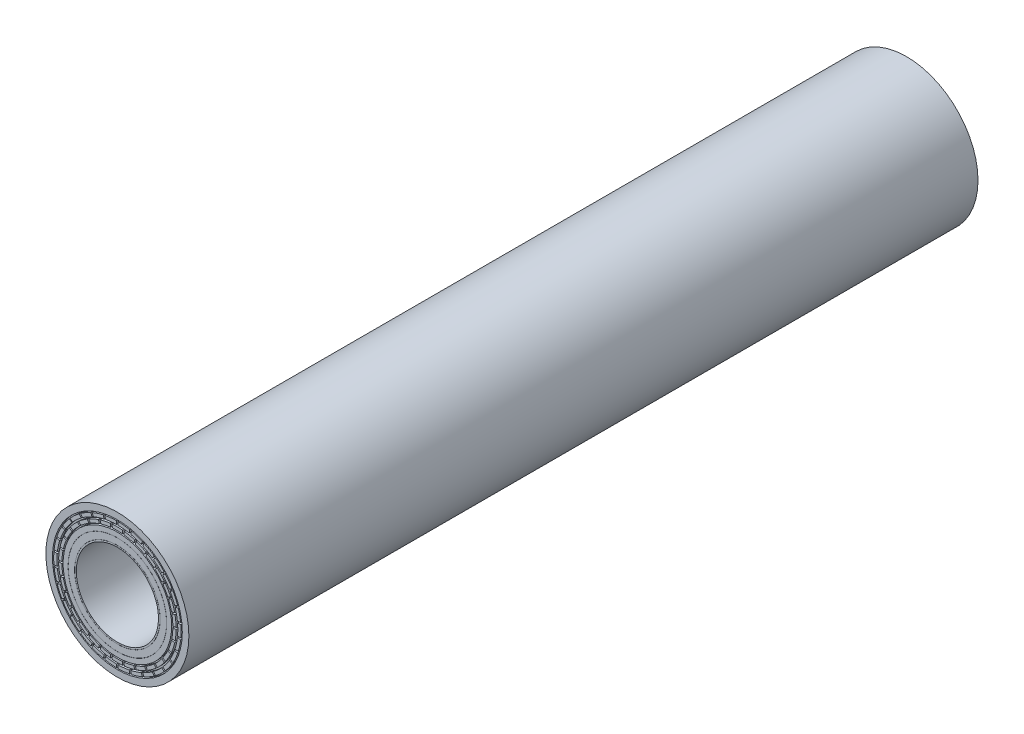
SolidWorks part; units mm, degrees
ref_plane "Front Plane" through (0, 0, 0) normal (0, 0, 1) x (1, 0, 0)
ref_plane "Top Plane" through (0, 0, 0) normal (0, 1, 0) x (1, 0, 0)
ref_plane "Right Plane" through (0, 0, 0) normal (1, 0, 0) x (0, 0, -1)
sketch "Sketch1" plane through (0, 0, 0) normal (0, 0, 1) x (1, 0, 0)
  circle A1 centre (0, 87) radius 87
  dimension "D1" = 87
  dimension "D2" = 0
  dimension "D3" = 174
extrude "Boss-Extrude1" add sketch "Sketch1" against normal blind 960
sketch "Sketch2" plane through (0, 0, 0) normal (0, 0, 1) x (1, 0, 0)
  circle A0 centre (0, 87) radius 52
  dimension "D1" = 104
extrude "Cut-Extrude1" cut sketch "Sketch2" against normal through all
sketch "Sketch3" plane through (0, 0, 0) normal (0, 0, 1) x (1, 0, 0)
  circle A0 centre (0, 87) radius 77.5
  circle A2 centre (0, 87) radius 87 construction
  circle A3 centre (0, 87) radius 60
  circle A4 centre (0, 87) radius 66
  circle A5 centre (0, 87) radius 67.5
  circle A6 centre (0, 87) radius 71.5
  circle A7 centre (0, 87) radius 73.5
  circle A8 centre (0, 87) radius 79
  dimension "D1" = 0
  dimension "D2" = 155
  dimension "D3" = 120
  dimension "D4" = 132
  dimension "D5" = 135
  dimension "D6" = 143
  dimension "D7" = 147
  dimension "D8" = 158
extrude "Cut-Extrude2" cut sketch "Sketch3" against normal blind 3 contours A8 A0 | A7 A6 | A5 A4
sketch "Sketch4" plane through (0, 0, 0) normal (0, 0, 1) x (1, 0, 0)
  circle A0 centre (0, 87) radius 60
  dimension "D1" = 120
split line "Split Line1"
ref_plane "Plane1" through (0, 0, -480) normal (0, 0, 1) x (1, 0, 0)
mirror "Mirror2" about plane through (0, 0, -480) normal (0, 0, 1) of "Cut-Extrude2"
sketch "Sketch5" plane through (0, 0, -960) normal (0, 0, -1) x (-1, 0, 0)
  circle A0 centre (0, 87) radius 60
  dimension "D1" = 120
split line "Split Line2"
sketch "Sketch7" plane through (0, 0, 0) normal (0, 0, 1) x (1, 0, 0)
  line L0 (0, 9) -> (0, 14.5)
  line L1 (-17.1953, 10.9124) -> (-16.0517, 16.2922)
  line L2 (-15.239, 10.4966) -> (-14.0954, 15.8764)
  line L3 (-16.2171, 10.7045) -> (-15.0736, 16.0843)
  line L4 (-16.0517, 16.2922) -> (-14.0954, 15.8764)
  line L5 (-17.1953, 10.9124) -> (-15.239, 10.4966)
  line L6 (-32.639, 16.1502) -> (-30.402, 21.1747)
  line L7 (-30.8119, 15.3367) -> (-28.5749, 20.3612)
  line L8 (-31.7255, 15.7435) -> (-29.4884, 20.768)
  line L9 (-30.402, 21.1747) -> (-28.5749, 20.3612)
  line L10 (-32.639, 16.1502) -> (-30.8119, 15.3367)
  line L11 (-46.6563, 24.4845) -> (-43.4234, 28.9341)
  line L12 (-45.0382, 23.3089) -> (-41.8054, 27.7585)
  line L13 (-45.8472, 23.8967) -> (-42.6144, 28.3463)
  line L14 (-43.4234, 28.9341) -> (-41.8054, 27.7585)
  line L15 (-46.6563, 24.4845) -> (-45.0382, 23.3089)
  line L16 (-58.6344, 35.551) -> (-54.5471, 39.2312)
  line L17 (-57.2962, 34.0647) -> (-53.2089, 37.7449)
  line L18 (-57.9653, 34.8078) -> (-53.878, 38.488)
  line L19 (-54.5471, 39.2312) -> (-53.2089, 37.7449)
  line L20 (-58.6344, 35.551) -> (-57.2962, 34.0647)
  line L21 (-68.05, 48.866) -> (-63.2868, 51.616)
  line L22 (-67.05, 47.134) -> (-62.2868, 49.884)
  line L23 (-67.55, 48) -> (-62.7868, 50.75)
  line L24 (-63.2868, 51.616) -> (-62.2868, 49.884)
  line L25 (-68.05, 48.866) -> (-67.05, 47.134)
  line L26 (-74.4914, 63.8477) -> (-69.2606, 65.5473)
  line L27 (-73.8734, 61.9456) -> (-68.6426, 63.6452)
  line L28 (-74.1824, 62.8967) -> (-68.9516, 64.5963)
  line L29 (-69.2606, 65.5473) -> (-68.6426, 63.6452)
  line L31 (-74.4914, 63.8477) -> (-73.8734, 61.9456)
  line L32 (-77.6772, 79.8413) -> (-72.2074, 80.4162)
  line L33 (-77.4682, 77.8523) -> (-71.9983, 78.4272)
  line L34 (-77.5727, 78.8468) -> (-72.1028, 79.4217)
  line L35 (-72.2074, 80.4162) -> (-71.9983, 78.4272)
  line L36 (-77.6772, 79.8413) -> (-77.4682, 77.8523)
  line L37 (-77.4682, 96.1477) -> (-71.9983, 95.5728)
  line L38 (-77.6772, 94.1587) -> (-72.2074, 93.5838)
  line L39 (-77.5727, 95.1532) -> (-72.1028, 94.5783)
  line L40 (-71.9983, 95.5728) -> (-72.2074, 93.5838)
  line L41 (-77.4682, 96.1477) -> (-77.6772, 94.1587)
  line L42 (-73.8734, 112.0544) -> (-68.6426, 110.3548)
  line L43 (-74.4914, 110.1523) -> (-69.2606, 108.4527)
  line L44 (-74.1824, 111.1033) -> (-68.9516, 109.4037)
  line L45 (-68.6426, 110.3548) -> (-69.2606, 108.4527)
  line L46 (-73.8734, 112.0544) -> (-74.4914, 110.1523)
  line L47 (-67.05, 126.866) -> (-62.2868, 124.116)
  line L48 (-68.05, 125.134) -> (-63.2868, 122.384)
  line L49 (-67.55, 126) -> (-62.7868, 123.25)
  line L50 (-62.2868, 124.116) -> (-63.2868, 122.384)
  line L51 (-67.05, 126.866) -> (-68.05, 125.134)
  line L52 (-57.2962, 139.9353) -> (-53.2089, 136.2551)
  line L53 (-58.6344, 138.449) -> (-54.5471, 134.7688)
  line L54 (-57.9653, 139.1922) -> (-53.878, 135.512)
  line L55 (-53.2089, 136.2551) -> (-54.5471, 134.7688)
  line L56 (-57.2962, 139.9353) -> (-58.6344, 138.449)
  line L57 (-45.0382, 150.6911) -> (-41.8054, 146.2415)
  line L58 (-46.6563, 149.5155) -> (-43.4234, 145.0659)
  line L59 (-45.8472, 150.1033) -> (-42.6144, 145.6537)
  line L61 (-41.8054, 146.2415) -> (-43.4234, 145.0659)
  line L62 (-45.0382, 150.6911) -> (-46.6563, 149.5155)
  line L63 (-30.8119, 158.6633) -> (-28.5749, 153.6388)
  line L64 (-32.639, 157.8498) -> (-30.402, 152.8253)
  line L65 (-31.7255, 158.2565) -> (-29.4884, 153.232)
  line L66 (-28.5749, 153.6388) -> (-30.402, 152.8253)
  line L67 (-30.8119, 158.6633) -> (-32.639, 157.8498)
  line L68 (-15.239, 163.5034) -> (-14.0954, 158.1236)
  line L69 (-17.1953, 163.0876) -> (-16.0517, 157.7078)
  line L70 (-16.2171, 163.2955) -> (-15.0736, 157.9157)
  line L71 (-14.0954, 158.1236) -> (-16.0517, 157.7078)
  line L72 (-15.239, 163.5034) -> (-17.1953, 163.0876)
  line L73 (1, 165) -> (1, 159.5)
  line L74 (-1, 165) -> (-1, 159.5)
  line L75 (0, 165) -> (0, 159.5)
  line L76 (1, 159.5) -> (-1, 159.5)
  line L77 (1, 165) -> (-1, 165)
  line L78 (17.1953, 163.0876) -> (16.0517, 157.7078)
  line L79 (15.239, 163.5034) -> (14.0954, 158.1236)
  line L80 (16.2171, 163.2955) -> (15.0736, 157.9157)
  line L81 (16.0517, 157.7078) -> (14.0954, 158.1236)
  line L82 (17.1953, 163.0876) -> (15.239, 163.5034)
  line L83 (32.639, 157.8498) -> (30.402, 152.8253)
  line L84 (30.8119, 158.6633) -> (28.5749, 153.6388)
  line L85 (31.7255, 158.2565) -> (29.4884, 153.232)
  line L86 (30.402, 152.8253) -> (28.5749, 153.6388)
  line L87 (32.639, 157.8498) -> (30.8119, 158.6633)
  line L88 (46.6563, 149.5155) -> (43.4234, 145.0659)
  line L89 (45.0382, 150.6911) -> (41.8054, 146.2415)
  line L90 (45.8472, 150.1033) -> (42.6144, 145.6537)
  line L91 (1, 9) -> (1, 14.5)
  line L92 (-1, 9) -> (-1, 14.5)
  line L93 (-1, 14.5) -> (1, 14.5)
  line L94 (-1, 9) -> (1, 9)
  line L95 (43.4234, 145.0659) -> (41.8054, 146.2415)
  line L96 (46.6563, 149.5155) -> (45.0382, 150.6911)
  line L97 (58.6344, 138.449) -> (54.5471, 134.7688)
  line L98 (57.2962, 139.9353) -> (53.2089, 136.2551)
  line L99 (57.9653, 139.1922) -> (53.878, 135.512)
  line L100 (54.5471, 134.7688) -> (53.2089, 136.2551)
  line L101 (58.6344, 138.449) -> (57.2962, 139.9353)
  line L102 (68.05, 125.134) -> (63.2868, 122.384)
  line L103 (67.05, 126.866) -> (62.2868, 124.116)
  line L104 (67.55, 126) -> (62.7868, 123.25)
  line L105 (63.2868, 122.384) -> (62.2868, 124.116)
  line L106 (68.05, 125.134) -> (67.05, 126.866)
  line L107 (74.4914, 110.1523) -> (69.2606, 108.4527)
  line L108 (73.8734, 112.0544) -> (68.6426, 110.3548)
  line L109 (74.1824, 111.1033) -> (68.9516, 109.4037)
  line L110 (69.2606, 108.4527) -> (68.6426, 110.3548)
  line L111 (74.4914, 110.1523) -> (73.8734, 112.0544)
  line L112 (77.6772, 94.1587) -> (72.2074, 93.5838)
  line L113 (77.4682, 96.1477) -> (71.9983, 95.5728)
  line L114 (77.5727, 95.1532) -> (72.1028, 94.5783)
  line L115 (72.2074, 93.5838) -> (71.9983, 95.5728)
  line L116 (77.6772, 94.1587) -> (77.4682, 96.1477)
  line L117 (77.4682, 77.8523) -> (71.9983, 78.4272)
  line L118 (77.6772, 79.8413) -> (72.2074, 80.4162)
  line L119 (77.5727, 78.8468) -> (72.1028, 79.4217)
  line L120 (71.9983, 78.4272) -> (72.2074, 80.4162)
  line L121 (77.4682, 77.8523) -> (77.6772, 79.8413)
  line L122 (73.8734, 61.9456) -> (68.6426, 63.6452)
  line L123 (74.4914, 63.8477) -> (69.2606, 65.5473)
  line L124 (74.1824, 62.8967) -> (68.9516, 64.5963)
  line L125 (68.6426, 63.6452) -> (69.2606, 65.5473)
  line L126 (73.8734, 61.9456) -> (74.4914, 63.8477)
  line L127 (67.05, 47.134) -> (62.2868, 49.884)
  line L128 (68.05, 48.866) -> (63.2868, 51.616)
  line L129 (67.55, 48) -> (62.7868, 50.75)
  line L130 (62.2868, 49.884) -> (63.2868, 51.616)
  line L131 (67.05, 47.134) -> (68.05, 48.866)
  line L132 (57.2962, 34.0647) -> (53.2089, 37.7449)
  line L133 (58.6344, 35.551) -> (54.5471, 39.2312)
  line L134 (57.9653, 34.8078) -> (53.878, 38.488)
  line L135 (53.2089, 37.7449) -> (54.5471, 39.2312)
  line L136 (57.2962, 34.0647) -> (58.6344, 35.551)
  line L137 (45.0382, 23.3089) -> (41.8054, 27.7585)
  line L138 (46.6563, 24.4845) -> (43.4234, 28.9341)
  line L139 (45.8472, 23.8967) -> (42.6144, 28.3463)
  line L140 (41.8054, 27.7585) -> (43.4234, 28.9341)
  line L141 (45.0382, 23.3089) -> (46.6563, 24.4845)
  line L142 (30.8119, 15.3367) -> (28.5749, 20.3612)
  line L143 (32.639, 16.1502) -> (30.402, 21.1747)
  line L144 (31.7255, 15.7435) -> (29.4884, 20.768)
  line L145 (28.5749, 20.3612) -> (30.402, 21.1747)
  line L146 (30.8119, 15.3367) -> (32.639, 16.1502)
  line L147 (15.239, 10.4966) -> (14.0954, 15.8764)
  line L148 (17.1953, 10.9124) -> (16.0517, 16.2922)
  line L149 (16.2171, 10.7045) -> (15.0736, 16.0843)
  line L150 (14.0954, 15.8764) -> (16.0517, 16.2922)
  line L151 (15.239, 10.4966) -> (17.1953, 10.9124)
  circle A5 centre (0, 87) radius 71.5 construction
  point P72 (0, 87)
  point P186 (0, 87)
  dimension "D1" = 1
  dimension "D2" = 1
  dimension "D3" = 72.5
  dimension "D4" = 30
extrude "Cut-Extrude5" cut sketch "Sketch7" against normal blind 3 contours L1 L5 L3 L4 | L3 L5 L2 L4 | L147 L151 L149 L150 | L149 L151 L148 L150 | L142 L146 L144 L145 | L144 L146 L143 L145 | L6 L10 L8 L9 | L8 L10 L7 L9 | L11 L15 L13 L14 | L13 L15 L12 L14 | L16 L20 L18 L19 | L21 L25 L23 L24 | L23 L25 L22 L24 | L26 L31 L28 L29 | L28 L31 L27 L29 | L32 L36 L34 L35 | L34 L36 L33 L35 | L37 L41 L39 L40 | L39 L41 L38 L40 | L42 L46 L44 L45 | L44 L46 L43 L45 | L49 L51 L48 L50 | L47 L51 L49 L50 | L54 L56 L53 L55 | L59 L62 L58 L61 | L57 L62 L59 L61 | L65 L67 L64 L66 | L63 L67 L65 L66 | L70 L72 L69 L71 | L68 L72 L70 L71 | L75 L77 L74 L76 | L73 L77 L75 L76 | L80 L82 L79 L81 | L78 L82 L80 L81 | L85 L87 L84 L86 | L83 L87 L85 L86 | L90 L96 L89 L95 | L88 L96 L90 L95 | L99 L101 L98 L100 | L97 L101 L99 L100 | L104 L106 L103 L105 | L102 L106 L104 L105 | L109 L111 L108 L110 | L107 L111 L109 L110 | L114 L116 L113 L115 | L112 L116 L114 L115 | L124 L126 L123 L125 | L122 L126 L124 L125 | L119 L121 L118 L120 | L117 L121 L119 L120 | L129 L131 L128 L130 | L127 L131 L129 L130 | L134 L136 L133 L135 | L132 L136 L134 L135 | L137 L141 L139 L140 | L139 L141 L138 L140 | L92 L94 L0 L93 | L0 L94 L91 L93
mirror "Mirror3" about plane through (0, 0, -480) normal (0, 0, 1) of "Cut-Extrude5"
sketch "Sketch8" plane through (0, 0, 0) normal (0, 0, 1) x (1, 0, 0)
  line L0 (-66.5, 88) -> (-72, 88)
  line L1 (-72, 88) -> (-72, 86)
  line L2 (-66.5, 86) -> (-72, 86)
  line L3 (-66.5, 88) -> (-66.5, 86)
  line L4 (-64.8389, 101.8043) -> (-70.2187, 102.9478)
  line L5 (-72, 87) -> (-66.5, 87) construction
  line L6 (-65.2547, 99.848) -> (-70.6345, 100.9915)
  line L7 (-64.8389, 101.8043) -> (-65.2547, 99.848)
  line L8 (-70.2187, 102.9478) -> (-70.6345, 100.9915)
  line L9 (-60.344, 114.9615) -> (-65.3685, 117.1986)
  line L10 (-61.1575, 113.1344) -> (-66.182, 115.3715)
  line L11 (-60.344, 114.9615) -> (-61.1575, 113.1344)
  line L12 (-65.3685, 117.1986) -> (-66.182, 115.3715)
  line L13 (-53.2118, 126.8967) -> (-57.6614, 130.1296)
  line L14 (-54.3874, 125.2787) -> (-58.837, 128.5115)
  line L15 (-53.2118, 126.8967) -> (-54.3874, 125.2787)
  line L16 (-57.6614, 130.1296) -> (-58.837, 128.5115)
  line L17 (-43.754, 137.0883) -> (-47.4343, 141.1756)
  line L18 (-45.2403, 135.75) -> (-48.9205, 139.8373)
  line L19 (-43.754, 137.0883) -> (-45.2403, 135.75)
  line L20 (-47.4343, 141.1756) -> (-48.9205, 139.8373)
  line L21 (-32.384, 145.0907) -> (-35.134, 149.8538)
  line L22 (-34.116, 144.0907) -> (-36.866, 148.8538)
  line L23 (-32.384, 145.0907) -> (-34.116, 144.0907)
  line L24 (-35.134, 149.8538) -> (-36.866, 148.8538)
  line L25 (-19.5986, 150.5543) -> (-21.2982, 155.7851)
  line L26 (-21.5007, 149.9362) -> (-23.2003, 155.1671)
  line L27 (-19.5986, 150.5543) -> (-21.5007, 149.9362)
  line L28 (-21.2982, 155.7851) -> (-23.2003, 155.1671)
  line L29 (-5.9566, 153.2402) -> (-6.5315, 158.7101)
  line L30 (-7.9457, 153.0312) -> (-8.5206, 158.501)
  line L31 (-5.9566, 153.2402) -> (-7.9457, 153.0312)
  line L32 (-6.5315, 158.7101) -> (-8.5206, 158.501)
  line L33 (7.9457, 153.0312) -> (8.5206, 158.501)
  line L34 (5.9566, 153.2402) -> (6.5315, 158.7101)
  line L35 (7.9457, 153.0312) -> (5.9566, 153.2402)
  line L36 (8.5206, 158.501) -> (6.5315, 158.7101)
  line L37 (21.5007, 149.9362) -> (23.2003, 155.1671)
  line L38 (19.5986, 150.5543) -> (21.2982, 155.7851)
  line L39 (21.5007, 149.9362) -> (19.5986, 150.5543)
  line L40 (23.2003, 155.1671) -> (21.2982, 155.7851)
  line L41 (34.116, 144.0907) -> (36.866, 148.8538)
  line L42 (32.384, 145.0907) -> (35.134, 149.8538)
  line L43 (34.116, 144.0907) -> (32.384, 145.0907)
  line L44 (36.866, 148.8538) -> (35.134, 149.8538)
  line L45 (45.2403, 135.75) -> (48.9205, 139.8373)
  line L46 (43.754, 137.0883) -> (47.4343, 141.1756)
  line L47 (45.2403, 135.75) -> (43.754, 137.0883)
  line L48 (48.9205, 139.8373) -> (47.4343, 141.1756)
  line L49 (54.3874, 125.2787) -> (58.837, 128.5115)
  line L50 (53.2118, 126.8967) -> (57.6614, 130.1296)
  line L51 (54.3874, 125.2787) -> (53.2118, 126.8967)
  line L52 (58.837, 128.5115) -> (57.6614, 130.1296)
  line L53 (61.1575, 113.1344) -> (66.182, 115.3715)
  line L54 (60.344, 114.9615) -> (65.3685, 117.1986)
  line L55 (61.1575, 113.1344) -> (60.344, 114.9615)
  line L56 (66.182, 115.3715) -> (65.3685, 117.1986)
  line L57 (65.2547, 99.848) -> (70.6345, 100.9915)
  line L58 (64.8389, 101.8043) -> (70.2187, 102.9478)
  line L59 (65.2547, 99.848) -> (64.8389, 101.8043)
  line L60 (70.6345, 100.9915) -> (70.2187, 102.9478)
  line L61 (66.5, 86) -> (72, 86)
  line L62 (66.5, 88) -> (72, 88)
  line L63 (66.5, 86) -> (66.5, 88)
  line L64 (72, 86) -> (72, 88)
  line L65 (64.8389, 72.1957) -> (70.2187, 71.0522)
  line L66 (65.2547, 74.152) -> (70.6345, 73.0085)
  line L67 (64.8389, 72.1957) -> (65.2547, 74.152)
  line L68 (70.2187, 71.0522) -> (70.6345, 73.0085)
  line L69 (60.344, 59.0385) -> (65.3685, 56.8014)
  line L70 (61.1575, 60.8656) -> (66.182, 58.6285)
  line L71 (60.344, 59.0385) -> (61.1575, 60.8656)
  line L72 (65.3685, 56.8014) -> (66.182, 58.6285)
  line L73 (53.2118, 47.1033) -> (57.6614, 43.8704)
  line L74 (54.3874, 48.7213) -> (58.837, 45.4885)
  line L75 (53.2118, 47.1033) -> (54.3874, 48.7213)
  line L76 (57.6614, 43.8704) -> (58.837, 45.4885)
  line L77 (43.754, 36.9117) -> (47.4343, 32.8244)
  line L78 (45.2403, 38.25) -> (48.9205, 34.1627)
  line L79 (43.754, 36.9117) -> (45.2403, 38.25)
  line L80 (47.4343, 32.8244) -> (48.9205, 34.1627)
  line L81 (32.384, 28.9093) -> (35.134, 24.1462)
  line L82 (34.116, 29.9093) -> (36.866, 25.1462)
  line L83 (32.384, 28.9093) -> (34.116, 29.9093)
  line L84 (35.134, 24.1462) -> (36.866, 25.1462)
  line L85 (19.5986, 23.4457) -> (21.2982, 18.2149)
  line L86 (21.5007, 24.0638) -> (23.2003, 18.8329)
  line L87 (19.5986, 23.4457) -> (21.5007, 24.0638)
  line L88 (21.2982, 18.2149) -> (23.2003, 18.8329)
  line L89 (5.9566, 20.7598) -> (6.5315, 15.2899)
  line L90 (7.9457, 20.9688) -> (8.5206, 15.499)
  line L91 (5.9566, 20.7598) -> (7.9457, 20.9688)
  line L92 (6.5315, 15.2899) -> (8.5206, 15.499)
  line L93 (-7.9457, 20.9688) -> (-8.5206, 15.499)
  line L94 (-5.9566, 20.7598) -> (-6.5315, 15.2899)
  line L95 (-7.9457, 20.9688) -> (-5.9566, 20.7598)
  line L96 (-8.5206, 15.499) -> (-6.5315, 15.2899)
  line L97 (-21.5007, 24.0638) -> (-23.2003, 18.8329)
  line L98 (-19.5986, 23.4457) -> (-21.2982, 18.2149)
  line L99 (-21.5007, 24.0638) -> (-19.5986, 23.4457)
  line L100 (-23.2003, 18.8329) -> (-21.2982, 18.2149)
  line L101 (-34.116, 29.9093) -> (-36.866, 25.1462)
  line L102 (-32.384, 28.9093) -> (-35.134, 24.1462)
  line L103 (-34.116, 29.9093) -> (-32.384, 28.9093)
  line L104 (-36.866, 25.1462) -> (-35.134, 24.1462)
  line L105 (-45.2403, 38.25) -> (-48.9205, 34.1627)
  line L106 (-43.754, 36.9117) -> (-47.4343, 32.8244)
  line L107 (-45.2403, 38.25) -> (-43.754, 36.9117)
  line L108 (-48.9205, 34.1627) -> (-47.4343, 32.8244)
  line L109 (-54.3874, 48.7213) -> (-58.837, 45.4885)
  line L110 (-53.2118, 47.1033) -> (-57.6614, 43.8704)
  line L111 (-54.3874, 48.7213) -> (-53.2118, 47.1033)
  line L112 (-58.837, 45.4885) -> (-57.6614, 43.8704)
  line L113 (-61.1575, 60.8656) -> (-66.182, 58.6285)
  line L114 (-60.344, 59.0385) -> (-65.3685, 56.8014)
  line L115 (-61.1575, 60.8656) -> (-60.344, 59.0385)
  line L116 (-66.182, 58.6285) -> (-65.3685, 56.8014)
  line L117 (-65.2547, 74.152) -> (-70.6345, 73.0085)
  line L118 (-64.8389, 72.1957) -> (-70.2187, 71.0522)
  line L119 (-65.2547, 74.152) -> (-64.8389, 72.1957)
  line L120 (-70.6345, 73.0085) -> (-70.2187, 71.0522)
  point P127 (0, 87)
  dimension "D1" = 30
extrude "Cut-Extrude6" cut sketch "Sketch8" against normal blind 3
mirror "Mirror4" about plane through (0, 0, -480) normal (0, 0, 1) of "Cut-Extrude6"
sketch "Sketch9" plane through (0, 0, 0) normal (0, 0, 1) x (1, 0, 0)
  circle A1 centre (0, 87) radius 50
  circle A2 centre (0, 87) radius 52 construction
  circle A3 centre (0, 87) radius 52
  dimension "D1" = 100
extrude "Boss-Extrude2" add sketch "Sketch9" against normal blind 960
sketch "Sketch10" plane through (0, 0, 0) normal (0, 0, 1) x (1, 0, 0)
  circle A0 centre (0, 87) radius 52
  circle A1 centre (0, 87) radius 51.9
  dimension "D1" = 104
  dimension "D2" = 0.1
sketch "Sketch11" plane through (0, 0, -960) normal (0, 0, -1) x (-1, 0, 0)
  circle A0 centre (0, 87) radius 52
  circle A1 centre (0, 87) radius 52.1
  dimension "D1" = 104
  dimension "D2" = 0.1
extrude "Cut-Extrude7" cut sketch "Sketch10" against normal blind 1
extrude "Cut-Extrude8" cut sketch "Sketch11" against normal blind 1
sketch "Sketch12" plane through (0, 0, -960) normal (0, 0, -1) x (-1, 0, 0)
  circle A0 centre (0, 87) radius 60
  circle A1 centre (0, 87) radius 59.9
  dimension "D1" = 120
  dimension "D2" = 0.1
extrude "Cut-Extrude9" cut sketch "Sketch12" against normal blind 1
mirror "Mirror6" about plane through (0, 0, -480) normal (0, 0, 1) of "Cut-Extrude9"
